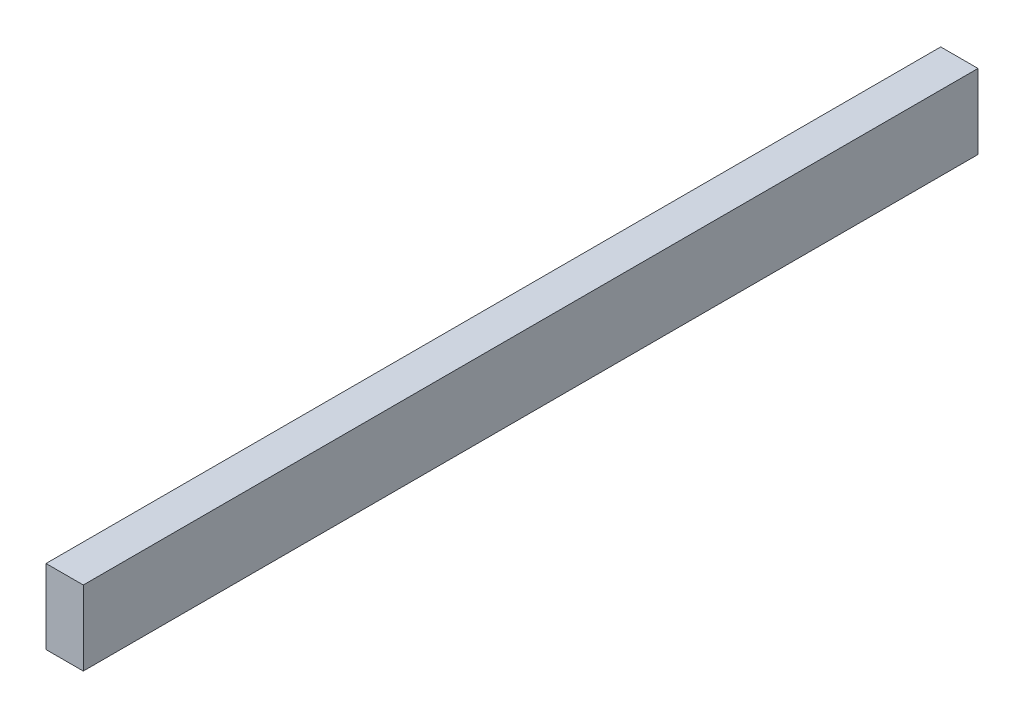
SolidWorks part; units mm, degrees
ref_plane "Front Plane" through (0, 0, 0) normal (0, 0, 1) x (1, 0, 0)
ref_plane "Top Plane" through (0, 0, 0) normal (0, 1, 0) x (1, 0, 0)
ref_plane "Right Plane" through (0, 0, 0) normal (1, 0, 0) x (0, 0, -1)
sketch "Sketch1" plane through (0, 0, 0) normal (0, 1, 0) x (1, 0, 0)
  line L1 (0, 0) -> (25.4, 0)
  line L2 (0, 0) -> (0, 609.6)
  line L3 (0, 609.6) -> (25.4, 609.6)
  line L4 (25.4, 0) -> (25.4, 609.6)
  dimension "D1" = 609.6
  dimension "D2" = 25.4
extrude "Boss-Extrude1" add sketch "Sketch1" along normal blind 50.8
